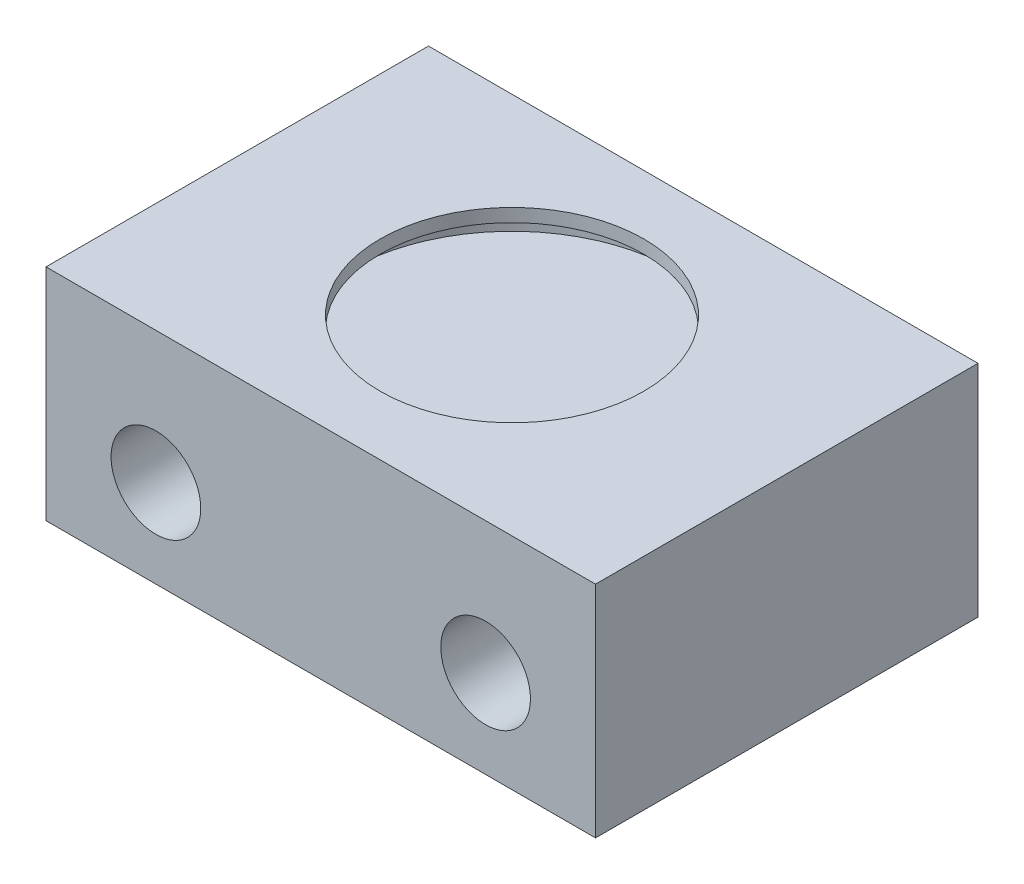
SolidWorks part; units mm, degrees
ref_plane "Front Plane" through (0, 0, 0) normal (0, 0, 1) x (1, 0, 0)
ref_plane "Top Plane" through (0, 0, 0) normal (0, 1, 0) x (1, 0, 0)
ref_plane "Right Plane" through (0, 0, 0) normal (1, 0, 0) x (0, 0, -1)
sketch "Sketch1" plane through (0, 0, 0) normal (0, 1, 0) x (1, 0, 0)
  line L1 (-15.875, 11.049) -> (15.875, 11.049)
  line L2 (-15.875, 11.049) -> (-15.875, -11.049)
  line L3 (-15.875, -11.049) -> (15.875, -11.049)
  line L4 (15.875, 11.049) -> (15.875, -11.049)
  line L5 (-15.875, 11.049) -> (15.875, -11.049) construction
  line L6 (-15.875, -11.049) -> (15.875, 11.049) construction
  point P0 (0, 0)
  dimension "D1" = 31.75
  dimension "D2" = 22.098
extrude "Boss-Extrude1" add sketch "Sketch1" along normal blind 12.7
ref_plane "Plane1" through (0, 10.16, 0) normal (0, 1, 0) x (1, 0, 0)
sketch "Sketch2" plane through (0, 10.16, 0) normal (0, 1, 0) x (1, 0, 0)
  circle A0 centre (0, 0) radius 9.525
  dimension "D1" = 19.05
extrude "Cut-Extrude1" cut sketch "Sketch2" along normal blind 1.778
hole_wizard "#6 (0.204) Diameter Hole1" positions "Sketch3" profile "Sketch4" hole size "#6" standard "ANSI Inch" end condition through all
sketch "Sketch3" plane through (0, 0, 11.049) normal (0, 0, 1) x (1, 0, 0)
  line L0 (-15.875, 0) -> (15.875, 0) construction
  line L1 (-9.525, 5.08) -> (9.525, 5.08)
  point P0 (-9.525, 5.08)
  point P2 (9.525, 5.08)
  point P14 (0, 5.08)
  dimension "D1" = 5.08
  dimension "D2" = 19.05
sketch "Sketch4" plane through (-9.525, 5.08, 11.049) normal (1, 0, 0) x (0, -1, 0)
  line L0 (0, 0) -> (0, 22.098)
  line L1 (0, 22.098) -> (2.5908, 22.098)
  line L2 (2.5908, 22.098) -> (2.5908, 0)
  line L5 (2.5908, 0) -> (0, 0)
  line L11 (0, -6.35) -> (0, 107.95) construction
  dimension "Thru Hole Dia." = 5.1816
  dimension "Thru Hole Depth" = 22.098
ref_plane "Plane2" through (-15.875, 12.7, 11.049) normal (0, -1, 0) x (-1, 0, 0)
sketch "Sketch5" plane through (0, 12.7, 0) normal (0, 1, 0) x (1, 0, 0)
  circle A0 centre (0, 0) radius 7.62
  dimension "D1" = 15.24
extrude "Cut-Extrude2" cut sketch "Sketch5" against normal up to next
